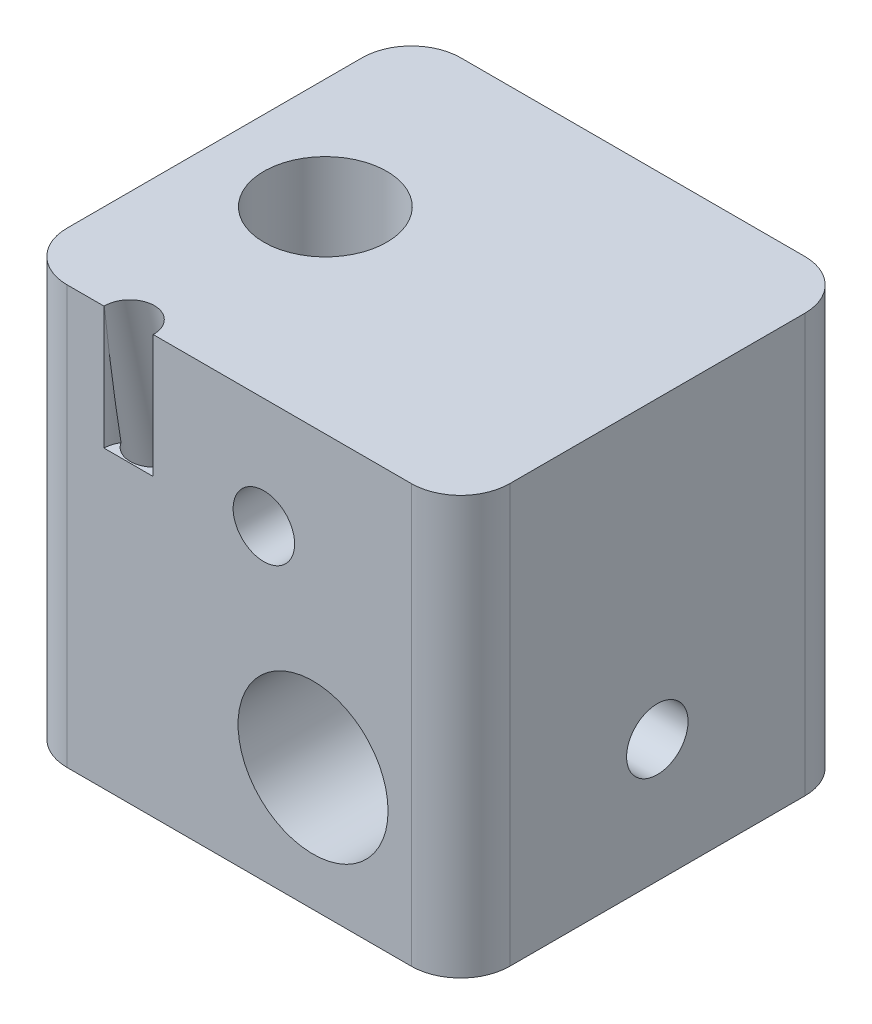
SolidWorks part; units mm, degrees
material "6061-T4 (SS)"
ref_plane "Front Plane" through (0, 0, 0) normal (0, 0, 1) x (1, 0, 0)
ref_plane "Top Plane" through (0, 0, 0) normal (0, 1, 0) x (1, 0, 0)
ref_plane "Right Plane" through (0, 0, 0) normal (1, 0, 0) x (0, 0, -1)
sketch "Sketch1" plane through (0, 0, 0) normal (0, 1, 0) x (1, 0, 0)
  line L0 (-9, 8) -> (9, -8) construction
  line L1 (-7, 8) -> (7, 8)
  line L2 (-9, 6) -> (-9, -6)
  line L3 (-7, -8) -> (7, -8)
  line L4 (9, 6) -> (9, -6)
  arc A0 (7, 8) -> (9, 6) centre (7, 6) cw
  arc A1 (7, -8) -> (9, -6) centre (7, -6) ccw
  arc A2 (-9, -6) -> (-7, -8) centre (-7, -6) ccw
  arc A3 (-7, 8) -> (-9, 6) centre (-7, 6) ccw
  point P7 (9, 8)
  point P13 (-9, -8)
  dimension "D3" = 2
  dimension "D1" = 18
  dimension "D2" = 16
extrude "Boss-Extrude1" add sketch "Sketch1" along normal blind 17
sketch "Sketch2" plane through (0, 0, 8) normal (0, 0, 1) x (1, 0, 0)
  line L0 (-7, 0) -> (7, 0) construction
  line L1 (9, 17) -> (9, 0) construction
  circle A0 centre (3, 5) radius 3.05
  dimension "D1" = 6.1
  dimension "D2" = 5
  dimension "D3" = 6
extrude "Cut-Extrude1" cut sketch "Sketch2" against normal through all
hole_wizard "M3x0.5 Tapped Hole1" positions "Sketch4" profile "Sketch3" tap size "M3x0.5" standard "Ansi Metric" end condition through all
sketch "Sketch4" plane through (0, 0, 8) normal (0, 0, 1) x (1, 0, 0)
  line L0 (9, 17) -> (9, 0) construction
  line L1 (-7, 17) -> (7, 17) construction
  point P0 (1, 12.5)
  dimension "D1" = 8
  dimension "D2" = 4.5
sketch "Sketch3" plane through (1, 12.5, 8) normal (1, 0, 0) x (0, -1, 0)
  line L0 (0, 0) -> (0, 16)
  line L1 (0, 16) -> (1.25, 16)
  line L2 (1.25, 16) -> (1.25, 0)
  line L5 (1.25, 0) -> (0, 0)
  line L11 (0, -6.35) -> (0, 107.95) construction
  dimension "Thru Tap Drill Dia." = 2.5
  dimension "Thru Tap Drill Depth" = 16
cosmetic thread "Hole Thread1" parameters "D2"=3
hole_wizard "M6x1.0 Tapped Hole1" positions "Sketch6" profile "Sketch5" tap size "M6x1.0" standard "Ansi Metric" end condition through all
sketch "Sketch6" plane through (0, 17, 0) normal (0, 1, 0) x (-1, 0, 0)
  line L0 (9, -6) -> (9, 6) construction
  point P0 (4.5, 0)
  dimension "D1" = 4.5
sketch "Sketch5" plane through (-4.5, 17, 0) normal (1, 0, 0) x (0, 0, 1)
  line L0 (0, 0) -> (0, 17)
  line L1 (0, 17) -> (2.5, 17)
  line L2 (2.5, 17) -> (2.5, 0)
  line L5 (2.5, 0) -> (0, 0)
  line L11 (0, -6.35) -> (0, 107.95) construction
  dimension "Thru Tap Drill Dia." = 5
  dimension "Thru Tap Drill Depth" = 17
cosmetic thread "Hole Thread2" parameters "D2"=6
sketch "Sketch7" plane through (0, 17, 0) normal (0, 1, 0) x (1, 0, 0)
  line L1 (-7, -8) -> (7, -8) construction
  circle A0 centre (-4.5, -8) radius 1
  dimension "D1" = 2
extrude "Cut-Extrude2" cut sketch "Sketch7" against normal blind 5
ref_plane "Plane1" through (-4.5, 0, 0) normal (-1, 0, 0) x (0, 0, 1)
sketch "Sketch8" plane through (-4.5, 0, 0) normal (-1, 0, 0) x (0, 0, 1)
  line L0 (4.6062, 1.1327) -> (8.0049, 17.1225) construction
  line L1 (4.7969, 2.0302) -> (5.9, 2.41)
  line L2 (5.9, 2.41) -> (9.2734, 18.2807)
  line L3 (9.2734, 18.2807) -> (8.2953, 18.4886)
  line L4 (8.2953, 18.4886) -> (4.7969, 2.0302)
  line L5 (-6, 0) -> (6, 0) construction
  line L6 (8, 17) -> (8, 0) construction
  line L7 (0, 0) -> (0, 17) construction
  dimension "D1" = 2.41
  dimension "D2" = 2.1
  dimension "D3" = 12
  dimension "D4" = 2
  dimension "D5" = 59
revolve "Cut-Revolve1" cut sketch "Sketch8" angle 360 about L0
hole_wizard "M3x0.5 Tapped Hole2" positions "Sketch10" profile "Sketch9" tap size "M3x0.5" standard "Ansi Metric"
sketch "Sketch10" plane through (9, 0, 0) normal (1, 0, 0) x (0, 0, -1)
  line L0 (8, 5) -> (-8, 5) construction
  point P0 (0, 5)
sketch "Sketch9" plane through (9, 5, 0) normal (0, 1, 0) x (0, 0, -1)
  line L0 (0, 0) -> (0, 6.7511)
  line L1 (0, 6.7511) -> (1.25, 6)
  line L2 (1.25, 6) -> (1.25, 0)
  line L5 (1.25, 0) -> (0, 0)
  line L10 (0, 6.7511) -> (-1.25, 6) construction
  line L11 (0, -6.35) -> (0, 107.95) construction
  dimension "Tap Drill Dia." = 2.5
  dimension "Tap Drill Depth" = 6
  dimension "Drill Angle" = 118
cosmetic thread "Hole Thread3" parameters "D1"=3.2179, "D2"=3
